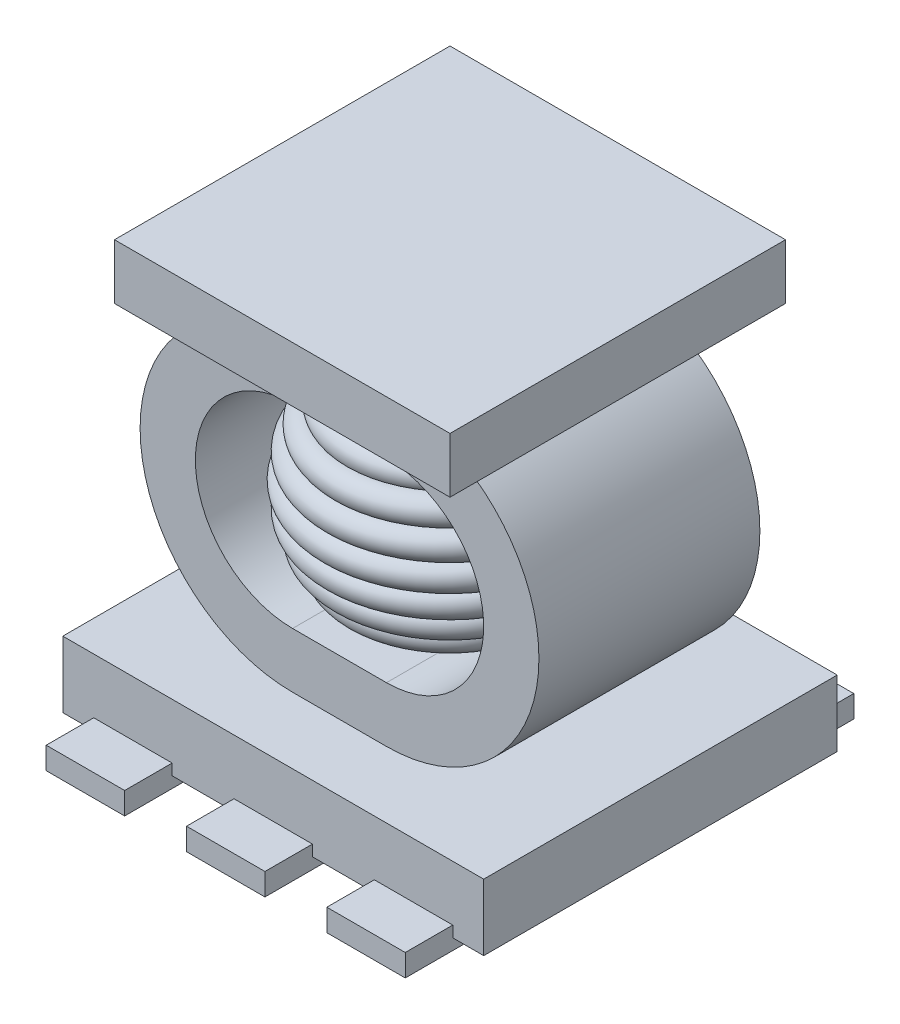
SolidWorks part; units mm, degrees
ref_plane "Спереди" through (0, 0, 0) normal (0, 0, 1) x (1, 0, 0)
ref_plane "Сверху" through (0, 0, 0) normal (0, 1, 0) x (1, 0, 0)
ref_plane "Справа" through (0, 0, 0) normal (1, 0, 0) x (0, 0, -1)
other "Configuration Table"
sketch "Sketch1" plane through (0, 0, 0) normal (0, 1, 0) x (1, 0, 0)
  line L1 (-1.905, 1.6) -> (1.905, 1.6)
  line L2 (-1.905, 1.6) -> (-1.905, -1.6)
  line L3 (-1.905, -1.6) -> (1.905, -1.6)
  line L4 (1.905, 1.6) -> (1.905, -1.6)
  line L5 (-1.905, 1.6) -> (1.905, -1.6) construction
  line L6 (-1.905, -1.6) -> (1.905, 1.6) construction
  point P0 (0, 0)
  dimension "D1" = 3.81
  dimension "D2" = 3.2
extrude "Boss-Extrude1" add sketch "Sketch1" along normal blind 0.6
sketch "Sketch2" plane through (0, 0, 0) normal (0, -1, 0) x (1, 0, 0)
  line L0 (0, 0) -> (0, 1.6) construction
  line L1 (-1.905, 1.6) -> (1.905, 1.6) construction
  line L2 (0, 0) -> (-1.905, 0) construction
  line L3 (-0.355, 1.1) -> (0.355, 1.1)
  line L4 (-0.355, 1.1) -> (-0.355, 2.03)
  line L5 (-0.355, 2.03) -> (0.355, 2.03)
  line L6 (0.355, 1.1) -> (0.355, 2.03)
  line L7 (-0.355, 1.1) -> (0.355, 2.03) construction
  line L8 (-0.355, 2.03) -> (0.355, 1.1) construction
  line L9 (-1.905, -1.6) -> (-1.905, 1.6) construction
  line L10 (1.625, 1.1) -> (0.915, 1.1)
  line L11 (-1.625, 2.03) -> (-0.915, 2.03)
  line L12 (-1.625, 2.03) -> (-1.625, 1.1)
  line L13 (-1.625, 1.1) -> (-0.915, 1.1)
  line L14 (-0.915, 2.03) -> (-0.915, 1.1)
  line L15 (0.915, 2.03) -> (0.915, 1.1)
  line L16 (1.625, 2.03) -> (0.915, 2.03)
  line L17 (1.625, 2.03) -> (1.625, 1.1)
  line L18 (-1.625, -1.1) -> (-0.915, -1.1)
  line L19 (-0.915, -2.03) -> (-0.915, -1.1)
  line L20 (-1.625, -2.03) -> (-0.915, -2.03)
  line L21 (-1.625, -2.03) -> (-1.625, -1.1)
  line L22 (-0.355, -2.03) -> (0.355, -2.03)
  line L23 (0.355, -1.1) -> (0.355, -2.03)
  line L24 (-0.355, -1.1) -> (0.355, -1.1)
  line L25 (-0.355, -1.1) -> (-0.355, -2.03)
  line L26 (1.625, -2.03) -> (1.625, -1.1)
  line L27 (1.625, -2.03) -> (0.915, -2.03)
  line L28 (0.915, -2.03) -> (0.915, -1.1)
  line L29 (1.625, -1.1) -> (0.915, -1.1)
  point P5 (0, 1.565)
  dimension "D1" = 4.06
  dimension "D2" = 0.71
  dimension "D3" = 1.1
  dimension "D4" = 1.27
extrude "Boss-Extrude2" add sketch "Sketch2" along normal mid plane 0.2
sketch "Sketch3" plane through (0, 0, 0) normal (0, 0, 1) x (1, 0, 0)
  line L0 (0.425, 1.98) -> (-0.425, 1.98) construction
  line L1 (0.425, 0.6) -> (-0.425, 0.6)
  line L2 (0.425, 3.36) -> (-0.425, 3.36)
  line L3 (-1.905, 0.6) -> (1.905, 0.6) construction
  line L4 (0.355, -0.1) -> (-0.355, -0.1) construction
  line L5 (1.905, 0.6) -> (1.905, 0) construction
  line L6 (0.425, 1.1) -> (-0.425, 1.1)
  line L7 (0.425, 2.86) -> (-0.425, 2.86)
  arc A0 (0.425, 0.6) -> (0.425, 3.36) centre (0.425, 1.98) ccw
  arc A1 (-0.425, 3.36) -> (-0.425, 0.6) centre (-0.425, 1.98) ccw
  arc A2 (-0.425, 2.86) -> (-0.425, 1.1) centre (-0.425, 1.98) ccw
  arc A3 (0.425, 1.1) -> (0.425, 2.86) centre (0.425, 1.98) ccw
  point P2 (0, 1.98)
  point P11 (1.6937, 2.03)
  point P14 (1.805, 1.98)
  dimension "D1" = 3.46
  dimension "D2" = 0.1
  dimension "D3" = 0.5
extrude "Boss-Extrude3" add sketch "Sketch3" along normal mid plane 2
sketch "Sketch4" plane through (0, 0, 0) normal (0, 0, 1) x (1, 0, 0)
  line L0 (0, 2.86) -> (0, 0) construction
  line L1 (0.425, 2.86) -> (-0.425, 2.86) construction
  line L2 (-0.5647, 2.8844) -> (-0.2441, 2.8844)
  line L3 (-0.2441, 2.8844) -> (-0.2441, 2.86)
  line L4 (1.305, 1.98) -> (-1.305, 1.98) construction
  line L5 (-0.5647, 1.0756) -> (-0.2441, 1.0756)
  line L6 (-0.2441, 1.0756) -> (-0.2441, 1.1)
  line L7 (-0.2441, 2.86) -> (0, 2.86)
  line L8 (0, 2.86) -> (0, 1.1)
  line L9 (-0.425, 1.1) -> (0.425, 1.1) construction
  line L10 (0, 1.1) -> (-0.2441, 1.1)
  arc A0 (-0.5647, 2.8844) -> (-0.7774, 2.7279) centre (-0.063, 1.98) ccw
  arc A1 (0.425, 1.1) -> (0.425, 2.86) centre (0.425, 1.98) ccw construction
  arc A2 (-0.425, 2.86) -> (-0.425, 1.1) centre (-0.425, 1.98) ccw construction
  arc A3 (-1.0904, 2.0992) -> (-1.0904, 1.8608) centre (-1.0422, 1.98) ccw
  arc A4 (-1.0904, 2.0992) -> (-1.0358, 2.3311) centre (-1.0162, 2.2041) cw
  arc A5 (-1.0358, 2.3311) -> (-0.9296, 2.5445) centre (-0.9396, 2.4163) cw
  arc A6 (-0.9296, 2.5445) -> (-0.7774, 2.7279) centre (-0.8164, 2.6054) cw
  arc A7 (-0.9296, 1.4155) -> (-0.7774, 1.2321) centre (-0.8164, 1.3546) ccw
  arc A8 (-1.0358, 1.6289) -> (-0.9296, 1.4155) centre (-0.9396, 1.5437) ccw
  arc A9 (-1.0904, 1.8608) -> (-1.0358, 1.6289) centre (-1.0162, 1.7559) ccw
  arc A10 (-0.7774, 1.2321) -> (-0.5647, 1.0756) centre (-0.063, 1.98) ccw
  arc A11 (-0.7774, 2.7279) -> (-0.9296, 2.5445) centre (-0.063, 1.98) ccw construction
  arc A12 (-0.9296, 2.5445) -> (-1.0358, 2.3311) centre (-0.063, 1.98) ccw construction
  arc A13 (-1.0358, 2.3311) -> (-1.0904, 2.0992) centre (-0.063, 1.98) ccw construction
  arc A14 (-1.0904, 2.0992) -> (-1.0973, 1.98) centre (-0.063, 1.98) ccw construction
  arc A15 (-1.0973, 1.98) -> (-1.0904, 1.8608) centre (-0.063, 1.98) ccw construction
  arc A16 (-1.0904, 1.8608) -> (-1.0358, 1.6289) centre (-0.063, 1.98) ccw construction
  arc A17 (-1.0358, 1.6289) -> (-0.9296, 1.4155) centre (-0.063, 1.98) ccw construction
  arc A18 (-0.9296, 1.4155) -> (-0.7774, 1.2321) centre (-0.063, 1.98) ccw construction
  point P32 (-1.0886, 2.3235)
  point P33 (-0.8614, 2.6953)
  point P41 (0, 0)
  point P42 (0, 0)
  point P43 (-0.7359, 2.7814)
  point P44 (-1.1209, 2.0938)
  point P45 (-0.7744, 2.7279)
  point P46 (-1.0904, 1.98)
revolve "Revolve1" add sketch "Sketch4" angle 360 about L8
sketch "Sketch6" plane through (0, 3.36, 0) normal (0, 1, 0) x (1, 0, 0)
  line L1 (-1.5185, 1.5185) -> (1.5185, 1.5185)
  line L2 (-1.5185, 1.5185) -> (-1.5185, -1.5185)
  line L3 (-1.5185, -1.5185) -> (1.5185, -1.5185)
  line L4 (1.5185, 1.5185) -> (1.5185, -1.5185)
  line L5 (-1.5185, 1.5185) -> (1.5185, -1.5185) construction
  line L6 (-1.5185, -1.5185) -> (1.5185, 1.5185) construction
  point P0 (0, 0)
  point P6 (1.405, 1.511)
  point P7 (1.5185, 1.5185)
extrude "Boss-Extrude4" add sketch "Sketch6" along normal blind 0.5
